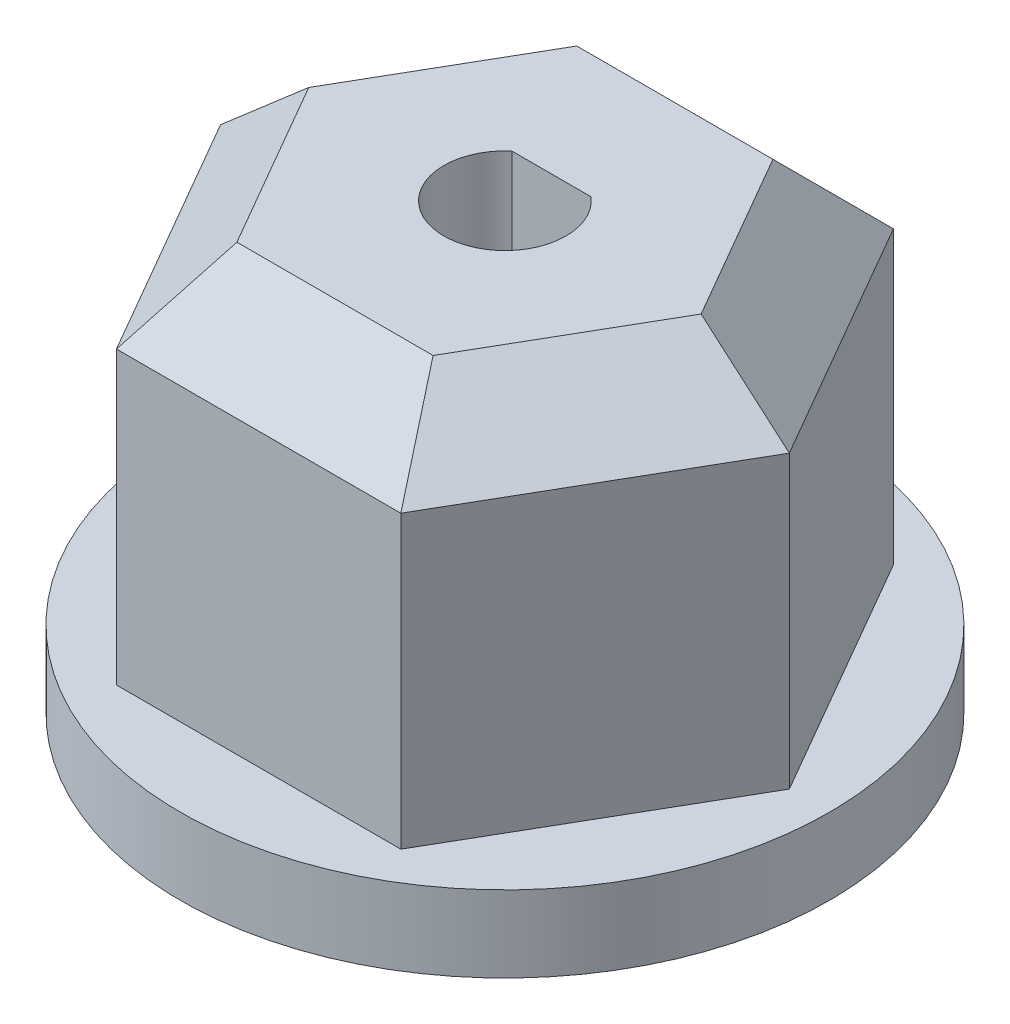
SolidWorks part; units mm, degrees
ref_plane "Front Plane" through (0, 0, 0) normal (0, 0, 1) x (1, 0, 0)
ref_plane "Top Plane" through (0, 0, 0) normal (0, 1, 0) x (1, 0, 0)
ref_plane "Right Plane" through (0, 0, 0) normal (1, 0, 0) x (0, 0, -1)
sketch "Sketch1" plane through (0, 0, 0) normal (0, 1, 0) x (1, 0, 0)
  line L0 (-1, 1.118) -> (1, 1.118) construction
  line L1 (7.3323, 0) -> (3.6662, 6.35) construction
  line L2 (3.6662, 6.35) -> (-3.6662, 6.35) construction
  line L3 (-3.6662, 6.35) -> (-7.3323, 0) construction
  line L4 (-7.3323, 0) -> (-3.6662, -6.35) construction
  line L5 (-3.6662, -6.35) -> (3.6662, -6.35) construction
  line L6 (3.6662, -6.35) -> (7.3323, 0) construction
  line L7 (3.7239, 6.45) -> (-3.7239, 6.45)
  line L8 (-3.7239, 6.45) -> (-7.4478, 0)
  line L9 (-7.4478, 0) -> (-3.7239, -6.45)
  line L10 (-3.7239, -6.45) -> (3.7239, -6.45)
  line L11 (3.7239, -6.45) -> (7.4478, 0)
  line L12 (7.4478, 0) -> (3.7239, 6.45)
  line L13 (-1.0375, 1.218) -> (1.0375, 1.218)
  circle A0 centre (0, 0) radius 6.35 construction
  arc A2 (-1, 1.118) -> (1, 1.118) centre (0, 0) ccw construction
  arc A3 (-1.0375, 1.218) -> (1.0375, 1.218) centre (0, 0) ccw
  point P11 (3.7482, 6.4921)
  dimension "D2" = 1.5
  dimension "D1" = 2
  dimension "D3" = 12.7
  dimension "D4" = 0.1
  dimension "D5" = 0.1
extrude "Boss-Extrude1" add sketch "Sketch1" along normal blind 7.62
sketch "Sketch2" plane through (0, 0, 0) normal (0, -1, 0) x (1, 0, 0)
  line L0 (1.0375, -1.218) -> (-1.0375, -1.218) construction
  line L1 (1.0375, -1.218) -> (-1.0375, -1.218)
  circle A0 centre (0, 0) radius 8.5
  arc A1 (1.0375, -1.218) -> (-1.0375, -1.218) centre (0, 0) ccw construction
  arc A2 (1.0375, -1.218) -> (-1.0375, -1.218) centre (0, 0) ccw
  dimension "D1" = 17
extrude "Boss-Extrude2" add sketch "Sketch2" along normal blind 2
sketch "Sketch3" plane through (0, 7.62, 0) normal (0, 1, 0) x (1, 0, 0)
  line L0 (1.0375, 1.218) -> (-1.0375, 1.218) construction
  line L1 (1.0375, 1.218) -> (-1.0375, 1.218)
  line L6 (7.4478, 0) -> (3.7239, 6.45)
  line L7 (3.7239, 6.45) -> (-3.7239, 6.45)
  line L8 (-3.7239, 6.45) -> (-7.4478, 0)
  line L9 (-7.4478, 0) -> (-3.7239, -6.45)
  line L10 (-3.7239, -6.45) -> (3.7239, -6.45)
  line L11 (3.7239, -6.45) -> (7.4478, 0)
  line L12 (7.4478, 0) -> (3.7239, 6.45)
  line L13 (3.7239, 6.45) -> (-3.7239, 6.45)
  line L14 (-3.7239, 6.45) -> (-7.4478, 0)
  line L15 (-7.4478, 0) -> (-3.7239, -6.45)
  line L16 (-3.7239, -6.45) -> (3.7239, -6.45)
  line L17 (3.7239, -6.45) -> (7.4478, 0)
  arc A0 (-1.0375, 1.218) -> (1.0375, 1.218) centre (0, 0) ccw construction
  arc A1 (-1.0375, 1.218) -> (1.0375, 1.218) centre (0, 0) ccw
  dimension "D1" = 0
extrude "Boss-Extrude3" add sketch "Sketch3" along normal blind 2
chamfer "Chamfer1" distance 2 angle 45 6 edges at (-5.5859, 9.62, -3.225) (0, 9.62, -6.45) (5.5859, 9.62, -3.225) (5.5859, 9.62, 3.225) (0, 9.62, 6.45) (-5.5859, 9.62, 3.225)
chamfer "Chamfer2" distance 1 angle 45 2 edges at (0, -2, -1.218) (0, -2, 1.6)
